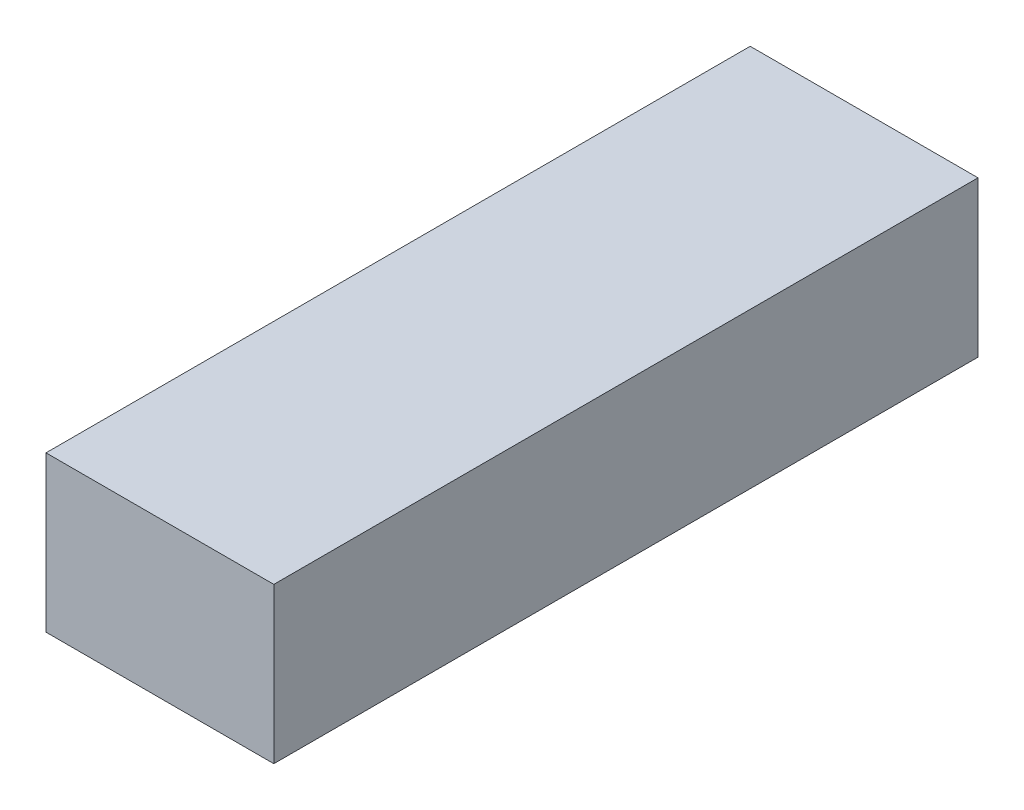
SolidWorks part; units mm, degrees
ref_plane "Front Plane" through (0, 0, 0) normal (0, 0, 1) x (1, 0, 0)
ref_plane "Top Plane" through (0, 0, 0) normal (0, 1, 0) x (1, 0, 0)
ref_plane "Right Plane" through (0, 0, 0) normal (1, 0, 0) x (0, 0, -1)
sketch "Sketch1" plane through (0, 0, 0) normal (0, 1, 0) x (1, 0, 0)
  line L1 (-21.1619, -87.6) -> (22.8381, -87.6)
  line L2 (-21.1619, -87.6) -> (-21.1619, 48.4)
  line L3 (-21.1619, 48.4) -> (22.8381, 48.4)
  line L4 (22.8381, -87.6) -> (22.8381, 48.4)
  dimension "D1" = 44
  dimension "D2" = 136
extrude "Boss-Extrude1" add sketch "Sketch1" along normal blind 30
